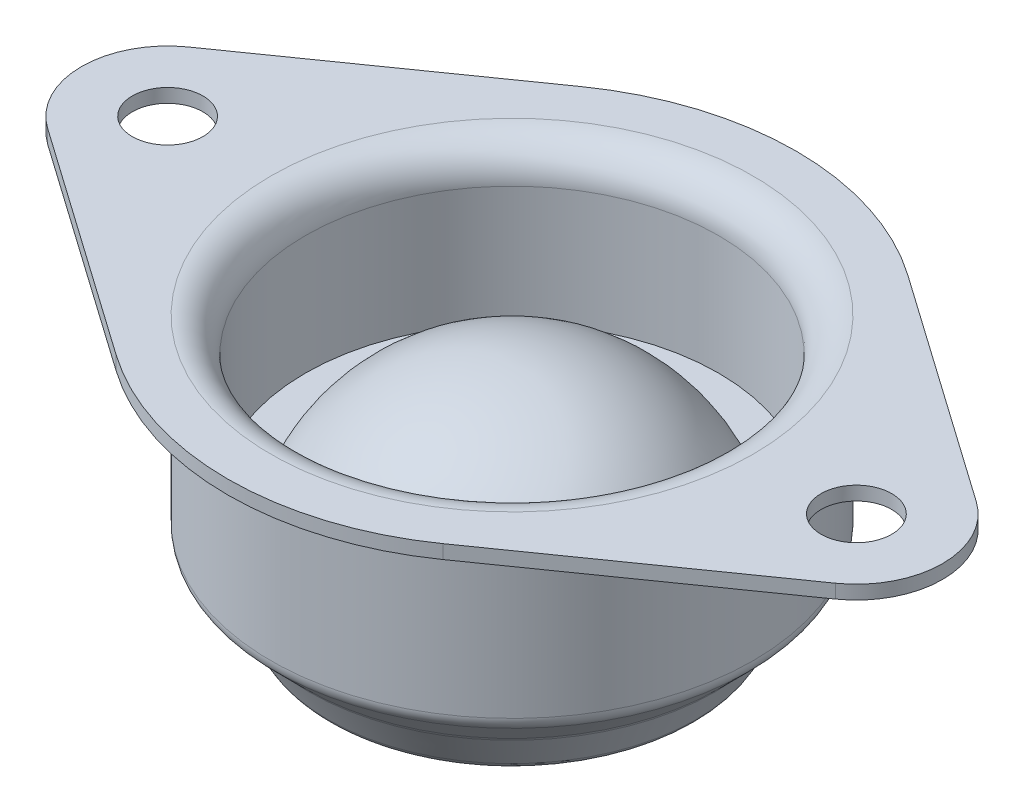
SolidWorks part; units mm, degrees
ref_plane "Ebene vorne" through (0, 0, 0) normal (0, 0, 1) x (1, 0, 0)
ref_plane "Ebene oben" through (0, 0, 0) normal (0, 1, 0) x (1, 0, 0)
ref_plane "Ebene rechts" through (0, 0, 0) normal (1, 0, 0) x (0, 0, -1)
sketch "Sketch1" plane through (0, 0, 0) normal (0, 0, 1) x (1, 0, 0)
  line L0 (14, 1.7) -> (14, -8.3)
  line L1 (14, -8.3) -> (11.8787, -10.4213)
  line L2 (11.8787, -10.4213) -> (10.3787, -13.0194)
  line L3 (7.223, -13.0194) -> (10.3787, -13.0194)
  line L4 (14, -8.3) -> (25.9913, -8.3) construction
  line L5 (12, 2.5) -> (12, -6.4174)
  line L6 (12, -6.4174) -> (10, -6.4174)
  line L7 (0, 43.2987) -> (0, -43.2987) construction
  line L8 (0, 0) -> (0, -18.5)
  line L9 (12, 2.5) -> (25, 2.5)
  line L11 (14, 1.7) -> (25, 1.7)
  line L12 (25, 2.5) -> (25, 1.7)
  arc A0 (10, -6.4174) -> (0, 0) centre (0, -11) ccw
  arc A1 (7.223, -13.0194) -> (0, -18.5) centre (0, -11) cw
  dimension "D1" = 7.5
  dimension "D2" = 28
  dimension "D10" = 11
  dimension "D3" = 2
  dimension "D4" = 2
  dimension "D5" = 10
  dimension "D6" = 0.8
  dimension "D7" = 50
  dimension "D9" = 21
  dimension "D11" = 2.5
  dimension "D12" = 135
  dimension "D13" = 120
  dimension "D14" = 3
  dimension "D15" = 3
revolve "Revolve1" add sketch "Sketch1" angle 360 about L7
fillet "Fillet1" radius 1 5 edges at (-7.223, -13.0194, 0) (-10.3787, -13.0194, 0) (-11.8787, -10.4213, 0) (-14, -8.3, 0) (-14, 1.7, 0)
fillet "Fillet2" radius 2 1 edges at (-12, 2.5, 0)
sketch "Sketch2" plane through (0, 2.5, 0) normal (0, 1, 0) x (1, 0, 0)
  line L0 (-22.875, 4.0908) -> (-9.4875, 13.4995)
  line L1 (-22.875, -4.0908) -> (-9.4875, -13.4995)
  line L2 (-29.7135, 0) -> (31.0312, 0) construction
  line L3 (0, 32.0477) -> (0, -34.8473) construction
  line L4 (22.875, -4.0908) -> (9.4875, -13.4995)
  line L5 (22.875, 4.0908) -> (9.4875, 13.4995)
  arc A0 (-9.4875, -13.4995) -> (-9.4875, 13.4995) centre (0, 0) ccw
  arc A1 (-22.875, 4.0908) -> (-22.875, -4.0908) centre (-20, 0) ccw
  circle A2 centre (0, 0) radius 25 construction
  arc A3 (22.875, 4.0908) -> (22.875, -4.0908) centre (20, 0) cw
  circle M6 centre (0, 0) radius 25
  dimension "D1" = 33
  dimension "D2" = 10
extrude "Cut-Extrude1" cut sketch "Sketch2" against normal up to next contours L5 A3 A1 L0 A0 M6 | A3 L4 A0 L1 A1 M6
hole_wizard "Ø4.1 (4.1) Diameter Hole1" positions "Sketch4" profile "Sketch5" hole size "Ø4.1" standard "DIN" end condition up to next
sketch "Sketch4" plane through (0, 2.5, 0) normal (0, 1, 0) x (1, 0, 0)
  point P0 (20, 0)
  point P3 (-20, 0)
sketch "Sketch5" plane through (20, 2.5, 0) normal (1, 0, 0) x (0, 0, 1)
  line L0 (0, 0) -> (0, 0.8)
  line L1 (0, 0.8) -> (2.05, 0.8)
  line L2 (2.05, 0.8) -> (2.05, 0)
  line L5 (2.05, 0) -> (0, 0)
  line L11 (0, -6.35) -> (0, 107.95) construction
  dimension "Thru Hole Dia." = 4.1
  dimension "Thru Hole Depth" = 0.8
